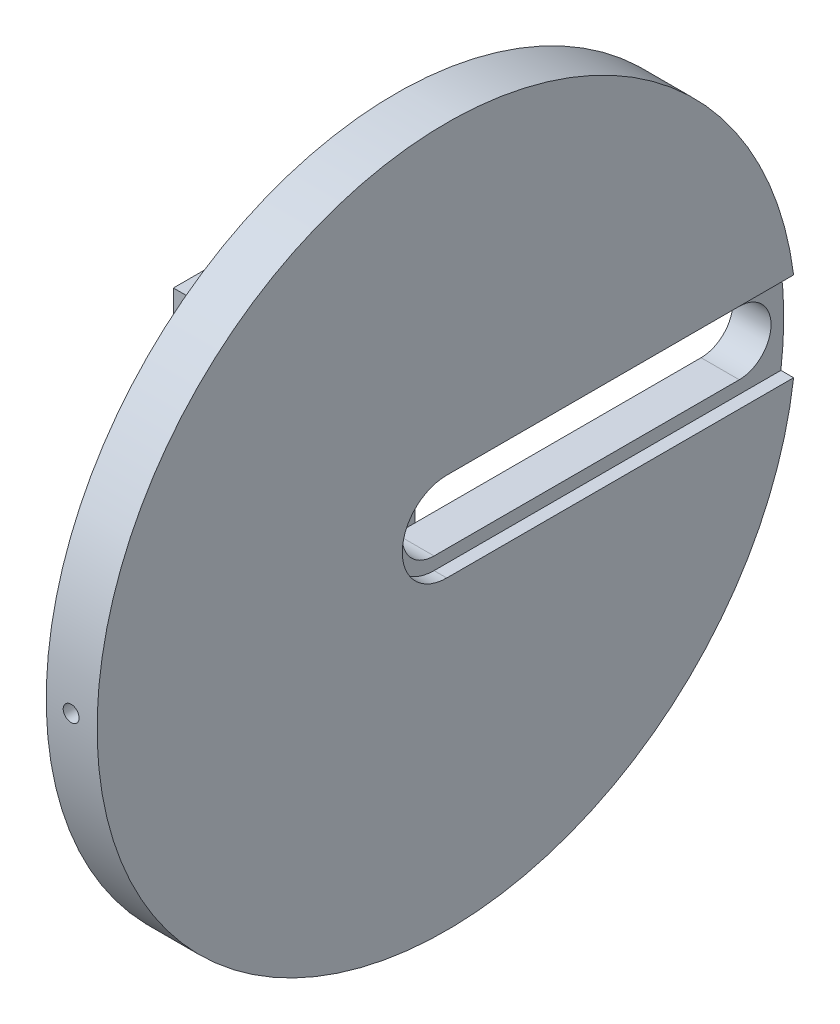
SolidWorks part; units mm, degrees
material "普通碳钢"
ref_plane "前视基准面" through (0, 0, 0) normal (0, 0, 1) x (1, 0, 0)
ref_plane "上视基准面" through (0, 0, 0) normal (0, 1, 0) x (1, 0, 0)
ref_plane "右视基准面" through (0, 0, 0) normal (1, 0, 0) x (0, 0, -1)
sketch "草图1" plane through (0, 0, 0) normal (1, 0, 0) x (0, 0, -1)
  circle A0 centre (0, 0) radius 7.5
  dimension "D1" = 15
extrude "凸台-拉伸1" add sketch "草图1" along normal blind 10
sketch "草图5" plane through (10, 0, 0) normal (1, 0, 0) x (0, 0, -1)
  line L1 (-15, -26) -> (15, -26)
  line L2 (-15, -26) -> (-15, 26)
  line L3 (-15, 26) -> (15, 26)
  line L4 (15, -26) -> (15, 26)
  line L5 (-15, -26) -> (15, 26) construction
  line L6 (-15, 26) -> (15, -26) construction
  point P0 (0, 0)
  dimension "D1" = 30
  dimension "D2" = 52
extrude "凸台-拉伸2" add sketch "草图5" along normal blind 8
sketch "草图6" plane through (18, 0, 0) normal (1, 0, 0) x (0, 0, -1)
  line L0 (15, -26) -> (15, 26) construction
  line L1 (-15, 26) -> (15, 26)
  line L2 (-15, 26) -> (-15, 18)
  line L3 (-15, 18) -> (15, 18)
  line L4 (15, 26) -> (15, 18)
  line L6 (-15, -26) -> (15, -26)
  line L7 (-15, -26) -> (-15, -18)
  line L8 (-15, -18) -> (15, -18)
  line L9 (15, -26) -> (15, -18)
  dimension "D1" = 8
  dimension "D2" = 8
extrude "凸台-拉伸3" add sketch "草图6" along normal blind 12
sketch "草图7" plane through (30, 0, 0) normal (1, 0, 0) x (0, 0, -1)
  circle A0 centre (0, 0) radius 55
  dimension "D1" = 110
extrude "凸台-拉伸4" add sketch "草图7" along normal blind 8 contours A0
sketch "草图8" plane through (38, 0, 0) normal (1, 0, 0) x (0, 0, -1)
  line L0 (0, 0) -> (48, 0) construction
  line L1 (0, 5) -> (48, 5)
  line L2 (0, -5) -> (48, -5)
  line L3 (0, -5) -> (40, -5) construction
  line L4 (0, 5) -> (40, 5) construction
  line L6 (0, 0) -> (40, 0) construction
  arc A0 (0, 5) -> (0, -5) centre (0, 0) ccw
  arc A2 (48, -5) -> (48, 5) centre (48, 0) ccw
  dimension "D3" = 48
  dimension "D4" = 5
extrude "切除-拉伸4" cut sketch "草图8" against normal up to next contours L1 A2 L2 A0
sketch "草图11" plane through (38, 0, 0) normal (1, 0, 0) x (0, 0, -1)
  line L0 (55, 0) -> (0, 0) construction
  line L2 (0, 7) -> (54.5527, 7)
  line L4 (0, -7) -> (54.5527, -7)
  arc A0 (0, 7) -> (0, -7) centre (0, 0) ccw
  circle A1 centre (0, 0) radius 55 construction
  arc A2 (54.5527, -7) -> (54.5527, 7) centre (0, 0) ccw
  dimension "D1" = 14
extrude "切除-拉伸6" cut sketch "草图11" against normal blind 2
sketch "草图12" plane through (0, 0, 0) normal (-1, 0, 0) x (0, 0, 1)
  circle A0 centre (0, 0) radius 9
  dimension "D1" = 18
extrude "切除-拉伸7" cut sketch "草图12" against normal up to next
ref_plane "基准面1" through (0, 0, 55) normal (0, 0, 1) x (1, 0, 0)
sketch "草图13" plane through (0, 0, 55) normal (0, 0, 1) x (1, 0, 0)
  circle A0 centre (33.9187, 0) radius 1.5
  dimension "D1" = 3
hole_wizard "M3 螺纹孔1" positions "3D草图1" profile "草图14" tap size "M3" standard "GB"
sketch3d "3D草图1"
  point P0 (33.9187, 0, 55)
  point P3 (33.9187, 0, 55)
  point P6 (0, 0, 0)
sketch "草图14" plane through (33.9187, 0, 55) normal (1, 0, 0) x (0, -1, 0)
  line L0 (0, 0) -> (0, 5.7511)
  line L1 (0, 5.7511) -> (1.25, 5)
  line L2 (1.25, 5) -> (1.25, 0)
  line L5 (1.25, 0) -> (0, 0)
  line L10 (0, 5.7511) -> (-1.25, 5) construction
  line L11 (0, -6.35) -> (0, 107.95) construction
  dimension "螺纹孔钻头直径" = 2.5
  dimension "螺纹孔钻头深度" = 5
  dimension "导头角度" = 118
cosmetic thread "孔螺蚊线1" parameters "D1"=5, "D2"=3
